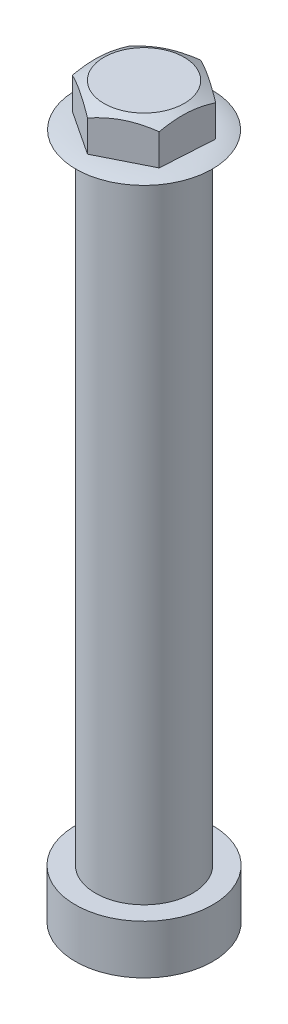
SolidWorks part; units mm, degrees
ref_plane "Front Plane" through (0, 0, 0) normal (0, 0, 1) x (1, 0, 0)
ref_plane "Top Plane" through (0, 0, 0) normal (0, 1, 0) x (1, 0, 0)
ref_plane "Right Plane" through (0, 0, 0) normal (1, 0, 0) x (0, 0, -1)
sketch "Sketch1" plane through (0, 0, 0) normal (0, 0, 1) x (1, 0, 0)
  line L0 (0, 0) -> (0, 19.1964) construction
  line L2 (2.5, 14.7321) -> (2.5, -18.0679)
  line L3 (2.5, -18.0679) -> (3.536, -18.0679)
  line L4 (3.536, -18.0679) -> (3.536, -20.5964)
  line L5 (3.536, -20.5964) -> (1.1679, -20.5964)
  line L6 (1.1679, -20.5964) -> (1.1679, -18.7294)
  line L7 (1.1679, -18.7294) -> (0, -17.5656)
  line L8 (0, -17.5656) -> (0, 14.9321)
  line L9 (2.5, 14.7321) -> (3.5151, 14.7321)
  line L10 (0, 14.9321) -> (2.3847, 14.9321)
  arc A1 (2.3847, 14.9321) -> (3.5151, 14.7321) centre (2.3428, 11.4008) cw
  dimension "D1" = 5
  dimension "D2" = 32.8
  dimension "D3" = 0.2
revolve "Revolve1" add sketch "Sketch1" angle 360 about L0
sketch "Sketch2" plane through (0, 14.9321, 0) normal (0, 1, 0) x (1, 0, 0)
  line L1 (2.4607, 1.2304) -> (0.1648, 2.7462)
  line L2 (0.1648, 2.7462) -> (-2.2959, 1.5159)
  line L3 (-2.2959, 1.5159) -> (-2.4607, -1.2304)
  line L4 (-2.4607, -1.2304) -> (-0.1648, -2.7462)
  line L5 (-0.1648, -2.7462) -> (2.2959, -1.5159)
  line L6 (2.2959, -1.5159) -> (2.4607, 1.2304)
  circle A0 centre (0, 0) radius 2.3826 construction
extrude "Boss-Extrude1" add sketch "Sketch2" along normal blind 2
sketch "Sketch3" plane through (0, 0, 0) normal (0, 0, 1) x (1, 0, 0)
  line L0 (1.4553, 17.2723) -> (3.2396, 16.2762)
  line L1 (3.2396, 16.2762) -> (3.2396, 17.2723)
  line L2 (3.2396, 17.2723) -> (1.4553, 17.2723)
  line L3 (0, 14.7321) -> (0, 18.5346) construction
  line L4 (-2.5, 14.7321) -> (2.5, 14.7321) construction
  point P2 (3.2396, 16.2762)
  point P4 (1.7337, 17.3763)
  point P10 (1.4553, 17.2723)
revolve "Cut-Revolve1" cut sketch "Sketch3" angle 360 about L3
